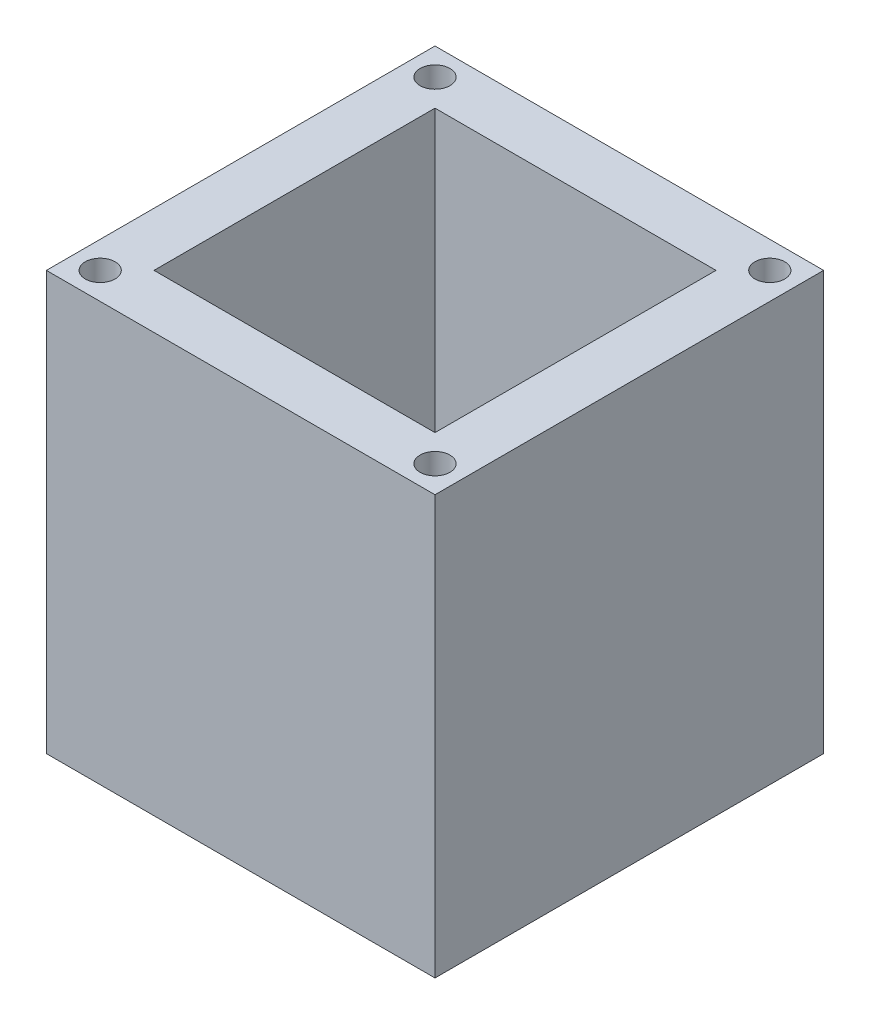
SolidWorks part; units mm, degrees
ref_plane "Front Plane" through (0, 0, 0) normal (0, 0, 1) x (1, 0, 0)
ref_plane "Top Plane" through (0, 0, 0) normal (0, 1, 0) x (1, 0, 0)
ref_plane "Right Plane" through (0, 0, 0) normal (1, 0, 0) x (0, 0, -1)
sketch "Sketch1" plane through (0, 0, 0) normal (0, 1, 0) x (1, 0, 0)
  line L1 (0, 0) -> (65, 0)
  line L2 (0, 0) -> (0, 65)
  line L3 (0, 65) -> (65, 65)
  line L4 (65, 0) -> (65, 65)
  dimension "D1" = 65
  dimension "D2" = 65
extrude "Boss-Extrude1" add sketch "Sketch1" along normal blind 70
sketch "Sketch2" plane through (0, 70, 0) normal (0, 1, 0) x (1, 0, 0)
  line L0 (0, 65) -> (0, 0) construction
  line L1 (9, 56) -> (56, 56)
  line L2 (9, 56) -> (9, 9)
  line L3 (9, 9) -> (56, 9)
  line L4 (56, 56) -> (56, 9)
  line L5 (65, 0) -> (65, 65) construction
  line L6 (65, 65) -> (0, 65) construction
  line L7 (0, 0) -> (65, 0) construction
  point P10 (60.2697, 65)
  dimension "D1" = 9
  dimension "D2" = 9
  dimension "D3" = 9
  dimension "D4" = 9
extrude "Cut-Extrude1" cut sketch "Sketch2" against normal blind 60
sketch "Sketch3" plane through (0, 0, 0) normal (0, -1, 0) x (1, 0, 0)
  line L0 (65, -65) -> (0, -65) construction
  line L1 (48.5, -48.5) -> (16.5, -48.5)
  line L2 (48.5, -48.5) -> (48.5, -16.5)
  line L3 (48.5, -16.5) -> (16.5, -16.5)
  line L4 (16.5, -48.5) -> (16.5, -16.5)
  line L5 (65, 0) -> (65, -65) construction
  point P4 (32.5, -48.5)
  point P7 (32.5, -65)
  point P8 (48.5, -32.5)
  point P11 (65, -32.5)
  dimension "D1" = 0
  dimension "D2" = 0
  dimension "D3" = 32
  dimension "D4" = 32
extrude "Cut-Extrude2" cut sketch "Sketch3" against normal blind 60
sketch "Sketch4" plane through (0, 70, 0) normal (0, 1, 0) x (1, 0, 0)
  line L0 (0, 65) -> (0, 0) construction
  line L1 (65, 65) -> (0, 65) construction
  line L2 (65, 0) -> (65, 65) construction
  line L3 (0, 0) -> (65, 0) construction
  circle A0 centre (4.5, 60.5) radius 2.5
  circle A1 centre (60.5, 60.5) radius 2.5
  circle A2 centre (60.5, 4.5) radius 2.5
  circle A3 centre (4.5, 4.5) radius 2.5
  dimension "D1" = 5
  dimension "D5" = 5
  dimension "D6" = 5
  dimension "D8" = 5
  dimension "D2" = 4.5
  dimension "D3" = 4.5
  dimension "D4" = 4.5
  dimension "D7" = 4.5
extrude "Cut-Extrude3" cut sketch "Sketch4" against normal blind 15
